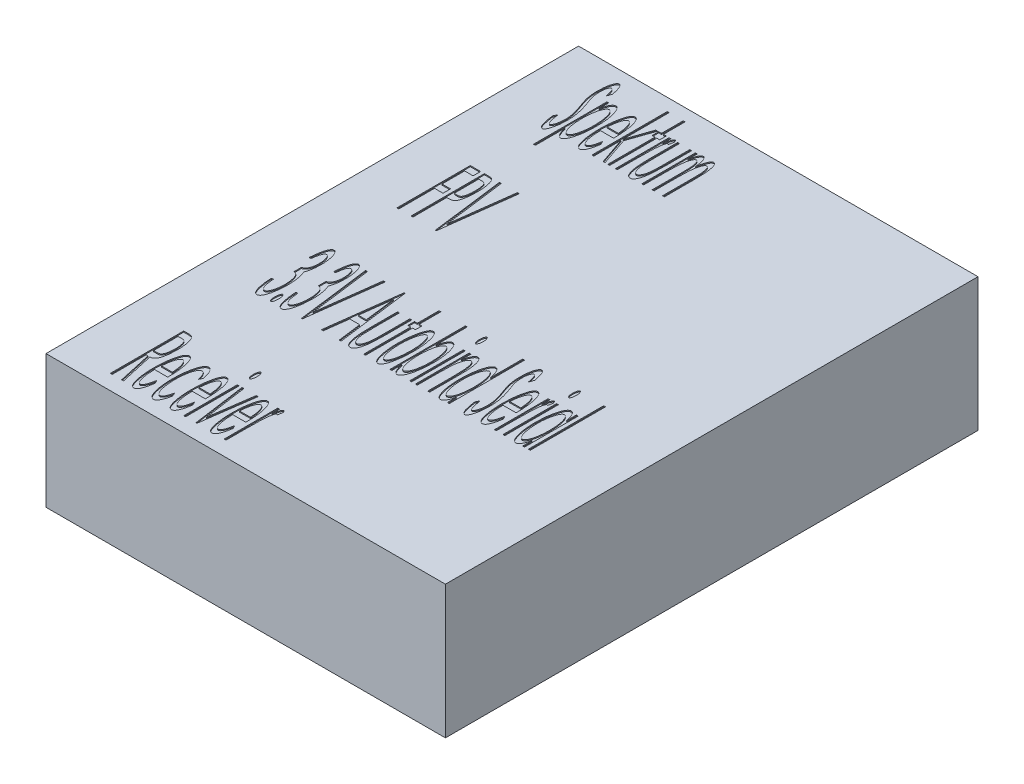
SolidWorks part; units mm, degrees
ref_plane "Front Plane" through (0, 0, 0) normal (0, 0, 1) x (1, 0, 0)
ref_plane "Top Plane" through (0, 0, 0) normal (0, 1, 0) x (1, 0, 0)
ref_plane "Right Plane" through (0, 0, 0) normal (1, 0, 0) x (0, 0, -1)
sketch "Sketch1" plane through (0, 0, 0) normal (0, 1, 0) x (1, 0, 0)
  line L1 (-9.525, 12.7) -> (9.525, 12.7)
  line L2 (-9.525, 12.7) -> (-9.525, -12.7)
  line L3 (-9.525, -12.7) -> (9.525, -12.7)
  line L4 (9.525, 12.7) -> (9.525, -12.7)
  line L5 (-9.525, 12.7) -> (9.525, -12.7) construction
  line L6 (-9.525, -12.7) -> (9.525, 12.7) construction
  point P0 (0, 0)
  dimension "D1" = 25.4
  dimension "D2" = 19.05
extrude "Boss-Extrude1" add sketch "Sketch1" along normal blind 6.35
sketch "Sketch2" plane through (0, 6.35, 0) normal (0, 1, 0) x (1, 0, 0)
  text T0 "Spektrum\r\nFPV\r\n3.3V Autobind Serial\r\nReceiver" font "Century Gothic" height 3.5
extrude "Cut-Extrude1" cut sketch "Sketch2" against normal blind 0.05
